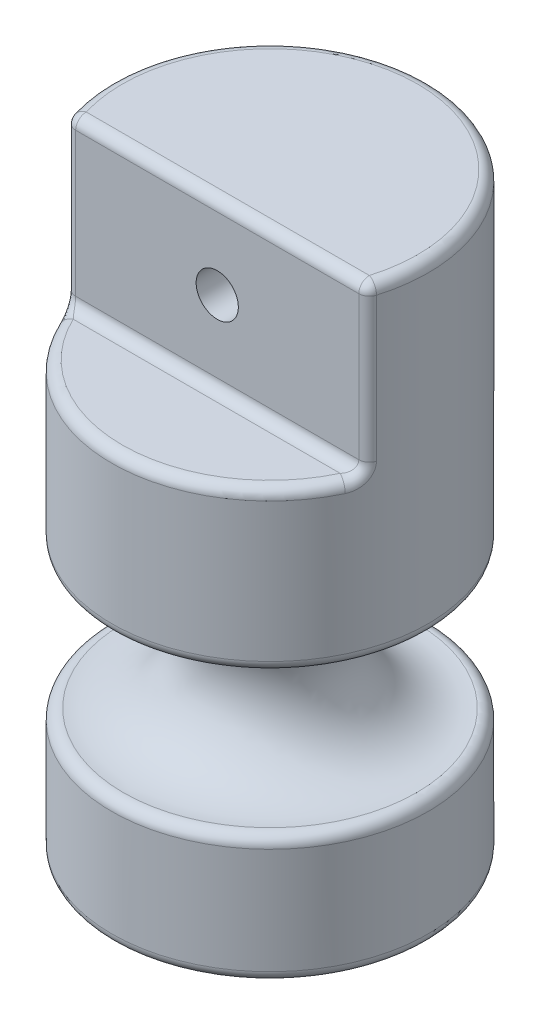
SolidWorks part; units mm, degrees
ref_plane "Front Plane" through (0, 0, 0) normal (0, 0, 1) x (1, 0, 0)
ref_plane "Top Plane" through (0, 0, 0) normal (0, 1, 0) x (1, 0, 0)
ref_plane "Right Plane" through (0, 0, 0) normal (1, 0, 0) x (0, 0, -1)
sketch "Sketch1" plane through (0, 0, 0) normal (0, 1, 0) x (1, 0, 0)
  circle A0 centre (0, 0) radius 7.62
  point P3 (0, 0)
  dimension "D1" = 15.24
extrude "Boss-Extrude1" add sketch "Sketch1" along normal blind 28.575
sketch "Sketch2" plane through (0, 0, 0) normal (0, 0, 1) x (1, 0, 0)
  line L5 (-7.62, 28.575) -> (-7.62, 0) construction
  line L7 (-7.62, 28.575) -> (-7.62, 0)
  line L8 (7.62, 28.575) -> (-7.62, 28.575) construction
  arc A0 (-7.62, 6.223) -> (-7.62, 12.827) centre (-6.6954, 9.525) ccw
  point P4 (0, 0)
  point P5 (0, 0)
  dimension "D2" = 6.858
  dimension "D1" = 19.05
  dimension "D4" = 6.604
ref_axis "Axis1" through (0, 28.575, 0) along (0, -1, 0)
revolve "Cut-Revolve1" cut sketch "Sketch2" angle 360 about axis through (0, 28.575, 0) along (0, -1, 0)
ref_plane "Plane1" through (0, 0, 2.54) normal (0, 0, 1) x (1, 0, 0)
sketch "Sketch3" plane through (0, 0, 2.54) normal (0, 0, 1) x (1, 0, 0)
  line L0 (-7.62, 28.575) -> (-7.62, 12.827) construction
  line L1 (7.62, 28.575) -> (-7.62, 28.575)
  line L2 (7.62, 28.575) -> (7.62, 20.6375)
  line L3 (7.62, 20.6375) -> (-7.62, 20.6375)
  line L4 (-7.62, 28.575) -> (-7.62, 20.6375)
  dimension "D1" = 7.9375
extrude "Cut-Extrude1" cut sketch "Sketch3" along normal through all
sketch "Sketch4" plane through (0, 0, 2.54) normal (0, 0, 1) x (1, 0, 0)
  point P0 (0, 24.6062)
hole_wizard "#4 (0.209) Diameter Hole1" positions "Sketch5" profile "Sketch6" hole size "#4" standard "ANSI Inch"
sketch "Sketch5" plane through (0, 0, 2.54) normal (0, 0, 1) x (1, 0, 0)
  point P0 (0, 24.6062)
sketch "Sketch6" plane through (0, 24.6062, 2.54) normal (1, 0, 0) x (0, -1, 0)
  line L0 (0, 0) -> (0, 6.9605)
  line L1 (0, 6.9605) -> (1.016, 6.35)
  line L2 (1.016, 6.35) -> (1.016, 0)
  line L5 (1.016, 0) -> (0, 0)
  line L10 (0, 6.9605) -> (-1.016, 6.35) construction
  line L11 (0, -6.35) -> (0, 107.95) construction
  dimension "Hole Dia." = 2.032
  dimension "Hole Depth" = 6.35
  dimension "Drill Angle" = 118
sketch "Sketch7" plane through (0, 0, 0) normal (0, -1, 0) x (-1, 0, 0)
  point P0 (0, 0)
hole_wizard "#10 (0.1935) Diameter Hole1" positions "Sketch8" profile "Sketch9" hole size "#10" standard "ANSI Inch"
sketch "Sketch8" plane through (0, 0, 0) normal (0, -1, 0) x (-1, 0, 0)
  point P0 (0, 0)
sketch "Sketch9" plane through (0, 0, 0) normal (1, 0, 0) x (0, 0, -1)
  line L0 (0, 0) -> (0, 7.4183)
  line L1 (0, 7.4183) -> (1.778, 6.35)
  line L2 (1.778, 6.35) -> (1.778, 0)
  line L5 (1.778, 0) -> (0, 0)
  line L10 (0, 7.4183) -> (-1.778, 6.35) construction
  line L11 (0, -6.35) -> (0, 107.95) construction
  dimension "Hole Dia." = 3.556
  dimension "Hole Depth" = 6.35
  dimension "Drill Angle" = 118
fillet "Fillet1" radius 0.508 9 edges at (-7.1842, 24.6062, 2.54) (7.1842, 24.6062, 2.54) (0, 28.575, -7.62) (0, 28.575, 2.54) (0, 20.6375, 2.54) (0, 20.6375, 7.62) (0, 0, 7.62) (0, 12.827, 7.62) (0, 6.223, 7.62)
